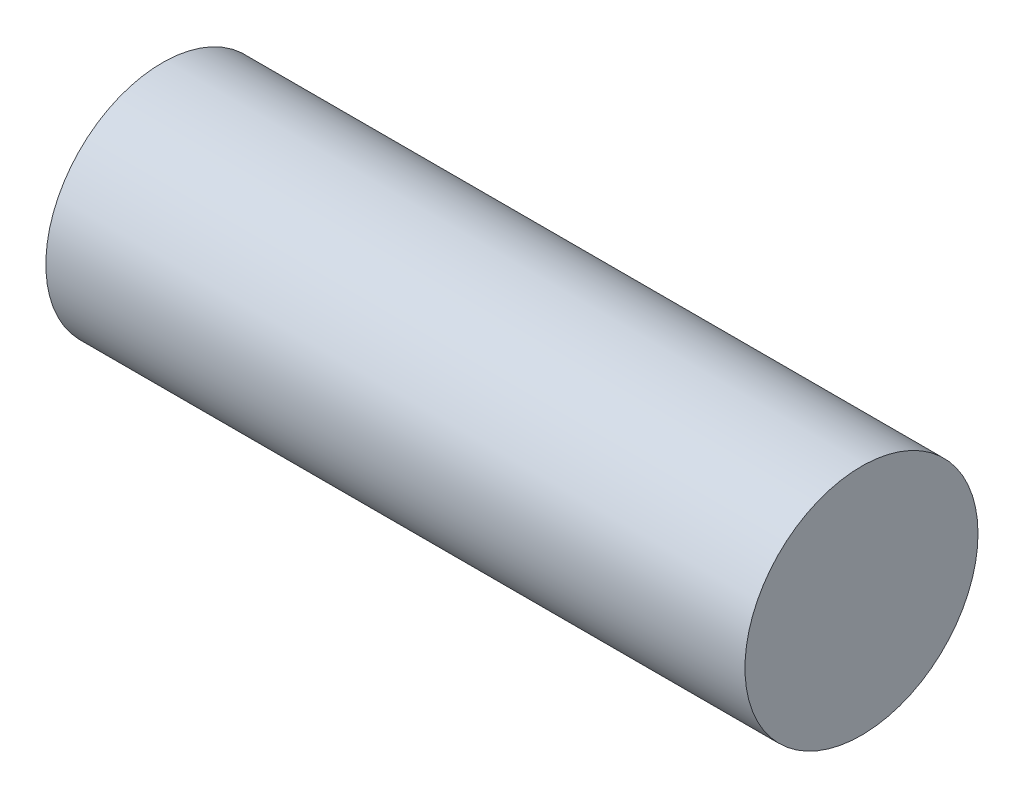
SolidWorks part; units mm, degrees
ref_plane "Front Plane" through (0, 0, 0) normal (0, 0, 1) x (1, 0, 0)
ref_plane "Top Plane" through (0, 0, 0) normal (0, 1, 0) x (1, 0, 0)
ref_plane "Right Plane" through (0, 0, 0) normal (1, 0, 0) x (0, 0, -1)
sketch "Sketch1" plane through (0, 0, 0) normal (1, 0, 0) x (0, 0, -1)
  circle A0 centre (0, 0) radius 0.635
  dimension "D1" = 1.27
extrude "Boss-Extrude1" add sketch "Sketch1" along normal blind 3.81
